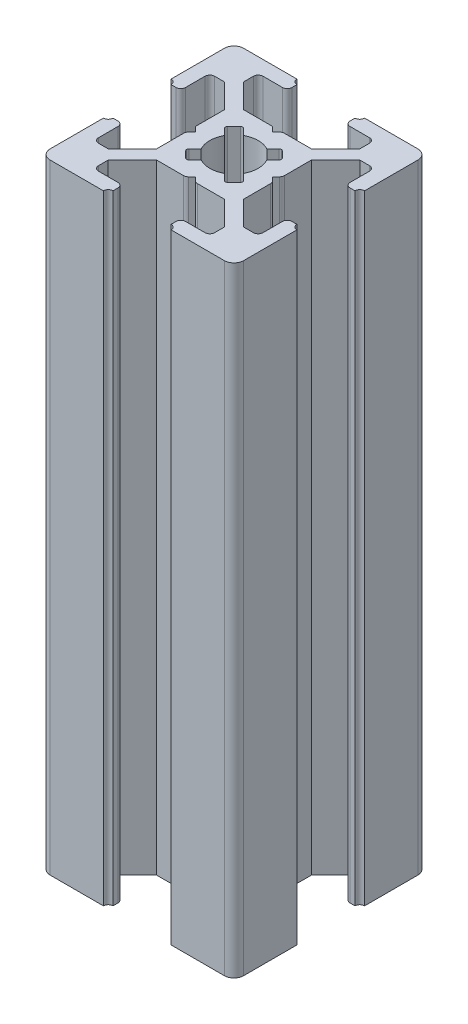
SolidWorks part; units mm, degrees
ref_plane "Front Plane" through (0, 0, 0) normal (0, 0, 1) x (1, 0, 0)
ref_plane "Top Plane" through (0, 0, 0) normal (0, 1, 0) x (1, 0, 0)
ref_plane "Right Plane" through (0, 0, 0) normal (1, 0, 0) x (0, 0, -1)
sketch "Sketch3" plane through (0, 0, 0) normal (0, 1, 0) x (1, 0, 0)
  line L0 (7, 20) -> (7, 18.5)
  line L1 (0, 0) -> (20, 0)
  line L2 (0, 0) -> (0, 20)
  line L3 (0, 20) -> (20, 20)
  line L4 (20, 0) -> (20, 20)
  line L5 (7, 18.5) -> (4, 18.5)
  line L6 (4, 18.5) -> (4, 17)
  line L7 (4, 17) -> (6.5, 14.5)
  line L8 (6.5, 14.5) -> (13.5, 14.5)
  line L9 (13.5, 14.5) -> (16, 17)
  line L10 (16, 17) -> (16, 18.5)
  line L11 (16, 18.5) -> (13, 18.5)
  line L12 (13, 18.5) -> (13, 20)
  line L13 (13, 20) -> (7, 20)
  line L14 (9.5, 14.5) -> (10, 14)
  line L15 (10, 14) -> (10.5, 14.5)
  line L16 (10.5, 14.5) -> (9.5, 14.5)
  line L17 (13, 19.5) -> (13, 20)
  line L18 (13.5, 20) -> (13, 20)
  line L19 (7, 19.5) -> (7, 20)
  line L20 (6.5, 20) -> (7, 20)
  line L21 (0, 13) -> (1.5, 13)
  line L22 (1.5, 13) -> (1.5, 16)
  line L23 (1.5, 16) -> (3, 16)
  line L24 (3, 16) -> (5.5, 13.5)
  line L25 (5.5, 13.5) -> (5.5, 6.5)
  line L26 (5.5, 6.5) -> (3, 4)
  line L27 (3, 4) -> (1.5, 4)
  line L28 (1.5, 4) -> (1.5, 7)
  line L29 (1.5, 7) -> (0, 7)
  line L30 (0, 7) -> (0, 13)
  line L31 (5.5, 10.5) -> (5.5, 9.5)
  line L32 (5.5, 9.5) -> (6, 10)
  line L33 (6, 10) -> (5.5, 10.5)
  line L34 (0.5, 13) -> (0, 13)
  line L35 (0, 13.5) -> (0, 13)
  line L36 (0, 6.5) -> (0, 7)
  line L37 (0.5, 7) -> (0, 7)
  line L38 (10, 20) -> (10, 0) construction
  line L39 (20, 10) -> (0, 10) construction
  line L40 (10, 6) -> (10.5, 5.5)
  line L41 (9.5, 5.5) -> (10, 6)
  line L42 (10.5, 5.5) -> (9.5, 5.5)
  line L43 (13.5, 0) -> (13, 0)
  line L44 (13, 0.5) -> (13, 0)
  line L45 (6.5, 0) -> (7, 0)
  line L46 (7, 0.5) -> (7, 0)
  line L47 (13, 1.5) -> (13, 0)
  line L48 (16, 1.5) -> (13, 1.5)
  line L49 (16, 3) -> (16, 1.5)
  line L50 (13.5, 5.5) -> (16, 3)
  line L51 (6.5, 5.5) -> (13.5, 5.5)
  line L52 (4, 3) -> (6.5, 5.5)
  line L53 (4, 1.5) -> (4, 3)
  line L54 (7, 1.5) -> (4, 1.5)
  line L55 (7, 0) -> (7, 1.5)
  line L56 (13, 0) -> (7, 0)
  line L57 (14.5, 9.5) -> (14, 10)
  line L58 (14.5, 10.5) -> (14.5, 9.5)
  line L59 (14, 10) -> (14.5, 10.5)
  line L60 (19.5, 7) -> (20, 7)
  line L61 (20, 6.5) -> (20, 7)
  line L62 (20, 13.5) -> (20, 13)
  line L63 (19.5, 13) -> (20, 13)
  line L64 (18.5, 7) -> (20, 7)
  line L65 (18.5, 4) -> (18.5, 7)
  line L66 (17, 4) -> (18.5, 4)
  line L67 (14.5, 6.5) -> (17, 4)
  line L68 (14.5, 13.5) -> (14.5, 6.5)
  line L69 (17, 16) -> (14.5, 13.5)
  line L70 (18.5, 16) -> (17, 16)
  line L71 (18.5, 13) -> (18.5, 16)
  line L72 (20, 13) -> (18.5, 13)
  line L73 (20, 7) -> (20, 13)
  arc A0 (13.5, 20) -> (13, 19.5) centre (13, 20) cw
  arc A1 (6.5, 20) -> (7, 19.5) centre (7, 20) ccw
  arc A2 (0.5, 13) -> (0, 13.5) centre (0, 13) ccw
  arc A3 (0.5, 7) -> (0, 6.5) centre (0, 7) cw
  arc A4 (13.5, 0) -> (13, 0.5) centre (13, 0) ccw
  arc A5 (6.5, 0) -> (7, 0.5) centre (7, 0) cw
  arc A6 (19.5, 7) -> (20, 6.5) centre (20, 7) ccw
  arc A7 (19.5, 13) -> (20, 13.5) centre (20, 13) cw
  point P7 (10, 14.5)
  point P16 (10, 20)
  point P26 (5.5, 10)
  point P35 (0, 10)
  dimension "D16" = 0.5
  dimension "D17" = 0.5
  dimension "D28" = 0.5
  dimension "D29" = 0.5
  dimension "D1" = 20
  dimension "D2" = 20
  dimension "D3" = 7
  dimension "D4" = 7
  dimension "D5" = 1.5
  dimension "D6" = 1.5
  dimension "D7" = 3
  dimension "D8" = 3
  dimension "D9" = 1.5
  dimension "D10" = 1.5
  dimension "D11" = 7
  dimension "D12" = 5.5
  dimension "D13" = 0.5
  dimension "D14" = 0.5
  dimension "D15" = 0.5
  dimension "D18" = 7
  dimension "D19" = 7
  dimension "D20" = 1.5
  dimension "D21" = 1.5
  dimension "D22" = 3
  dimension "D23" = 7
  dimension "D24" = 5.5
  dimension "D25" = 0.5
  dimension "D26" = 0.5
  dimension "D27" = 0.5
extrude "Boss-Extrude1" add sketch "Sketch3" along normal blind 64 contours L72 A7 L4 L3 A0 L12 L11 L10 L9 L8 L15 L14 L7 L6 L5 L0 A1 L2 A2 L21 L22 L23 L24 L25 L33 L32 L26 L27 L28 L29 A3 L1 A5 L55 L54 L53 L52 L51 L41 L40 L50 L49 L48 L47 A4
fillet "Fillet1" radius 1 4 edges at (0, 32, 0) (20, 32, 0) (20, 32, -20) (0, 32, -20)
sketch "Sketch4" plane through (0, 64, 0) normal (0, 1, 0) x (1, 0, 0)
  line L0 (13.5, 14.5) -> (5.5, 6.5) construction
  line L1 (14.5, 13.5) -> (6.5, 5.5) construction
  line L2 (10.5, 14.5) -> (14.5, 10.5) construction
  line L3 (12, 13) -> (13, 12)
  line L4 (13, 12) -> (8, 7)
  line L5 (8, 7) -> (7, 8)
  line L6 (7, 8) -> (12, 13)
  line L7 (13.5, 14.5) -> (16, 17) construction
  line L8 (17, 16) -> (14.5, 13.5) construction
  line L9 (5.5, 9.5) -> (9.5, 5.5) construction
  line L10 (5.5, 10.5) -> (9.5, 14.5) construction
  line L11 (14.5, 9.5) -> (10.5, 5.5) construction
  line L12 (6.5, 14.5) -> (14.5, 6.5) construction
  line L13 (5.5, 13.5) -> (13.5, 5.5) construction
  line L14 (7, 12) -> (8, 13)
  line L15 (8, 13) -> (13, 8)
  line L16 (13, 8) -> (12, 7)
  line L17 (12, 7) -> (7, 12)
  line L18 (4, 17) -> (6.5, 14.5) construction
  line L19 (3, 16) -> (5.5, 13.5) construction
  line L20 (20, 10) -> (0, 10) construction
  circle A0 centre (10, 10) radius 2.5
  dimension "D1" = 5
extrude "Cut-Extrude1" cut sketch "Sketch4" against normal through all contours L6 A0 L15 | L4 A0 L6 L15 | L15 A0 L17 L6 | L17 L4 L15 L6 | L17 A0 L6 | L6 A0 L4 L17 | L4 A0 L17 | L17 A0 L15 L4 | L15 A0 L4 | A0 L6 L5 L4 | A0 L17 L16 L15 | A0 L4 L3 L6 | A0 L15 L14 L17
fillet "Fillet2" radius 0.5 24 edges at (1.5, 32, -16) (1.5, 32, -13) (5.5, 32, -10.5) (5.5, 32, -9.5) (1.5, 32, -7) (1.5, 32, -4) (4, 32, -1.5) (7, 32, -1.5) (9.5, 32, -5.5) (10.5, 32, -5.5) (13, 32, -1.5) (16, 32, -1.5) (18.5, 32, -4) (18.5, 32, -7) (18.5, 32, -13) (18.5, 32, -16) (14.5, 32, -9.5) (14.5, 32, -10.5) (10.5, 32, -14.5) (9.5, 32, -14.5) (16, 32, -18.5) (13, 32, -18.5) (7, 32, -18.5) (4, 32, -18.5)
fillet "Fillet3" radius 0.25 8 edges at (13, 32, -8) (12, 32, -7) (13, 32, -12) (12, 32, -13) (8, 32, -13) (7, 32, -12) (7, 32, -8) (8, 32, -7)
